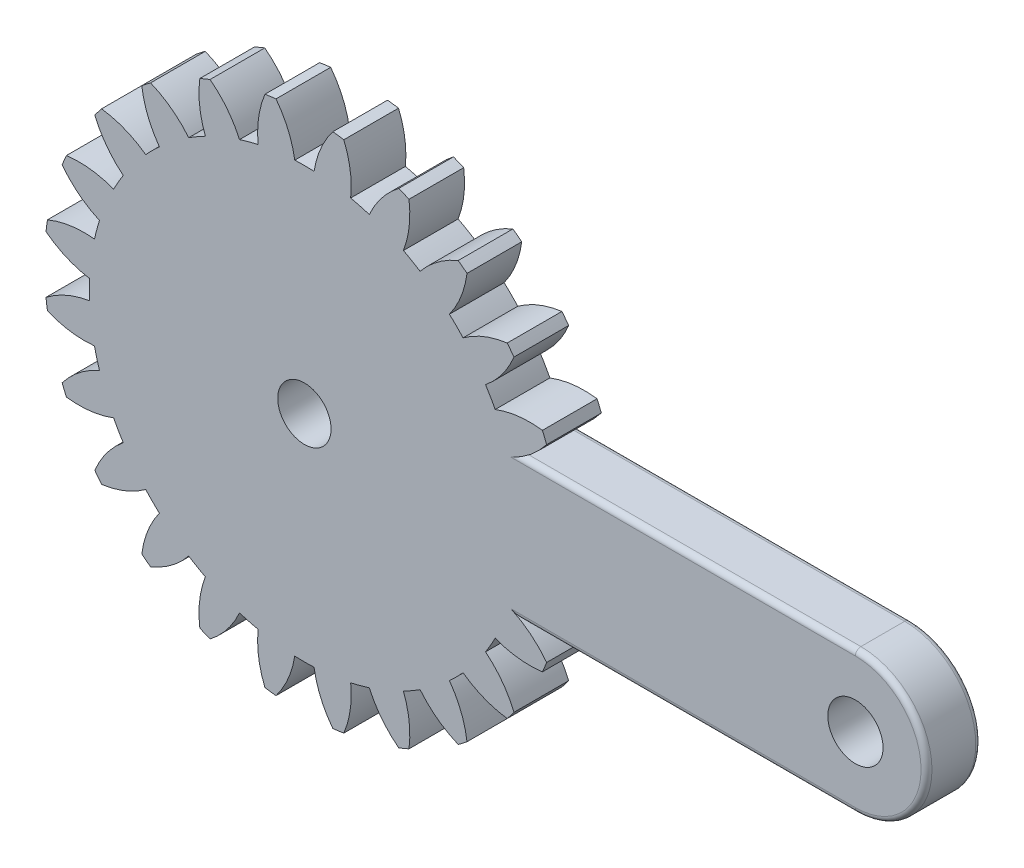
SolidWorks part; units mm, degrees
ref_plane "前视基准面" through (0, 0, 0) normal (0, 0, 1) x (1, 0, 0)
ref_plane "上视基准面" through (0, 0, 0) normal (0, 1, 0) x (1, 0, 0)
ref_plane "右视基准面" through (0, 0, 0) normal (1, 0, 0) x (0, 0, -1)
sketch "草图1" plane through (0, 0, 0) normal (0, 0, 1) x (1, 0, 0)
  line L4 (100.75, 13) -> (39.6109, 13)
  line L5 (39.6109, -13) -> (100.75, -13)
  circle A2 centre (100.75, 0) radius 5.05
  circle A3 centre (0, 0) radius 4.875
  arc A176 (100.75, -13) -> (100.75, 13) centre (100.75, 0) ccw
  arc A177 (39.6109, 13) -> (44.2913, 17.2482) centre (30.3487, 27.9068) ccw
  arc A178 (44.2913, 17.2482) -> (43.515, 19.1224) centre (0, 0) ccw
  arc A179 (43.515, 19.1224) -> (34.8837, 18.1034) centre (41.1928, 1.7267) ccw
  arc A180 (34.8837, 18.1034) -> (33.1198, 21.1585) centre (0, 0) ccw
  arc A181 (33.1198, 21.1585) -> (38.3179, 28.1239) centre (22.0918, 34.8107) ccw
  arc A182 (38.3179, 28.1239) -> (37.083, 29.7333) centre (0, 0) ccw
  arc A183 (37.083, 29.7333) -> (29.0095, 26.5151) centre (39.3423, 12.3293) ccw
  arc A184 (29.0095, 26.5151) -> (26.5151, 29.0095) centre (0, 0) ccw
  arc A185 (26.5151, 29.0095) -> (29.7333, 37.083) centre (12.3293, 39.3423) ccw
  arc A186 (29.7333, 37.083) -> (28.1239, 38.3179) centre (0, 0) ccw
  arc A187 (28.1239, 38.3179) -> (21.1585, 33.1198) centre (34.8107, 22.0918) ccw
  arc A188 (21.1585, 33.1198) -> (18.1034, 34.8837) centre (0, 0) ccw
  arc A189 (18.1034, 34.8837) -> (19.1224, 43.515) centre (1.7267, 41.1928) ccw
  arc A190 (19.1224, 43.515) -> (17.2482, 44.2913) centre (0, 0) ccw
  arc A191 (17.2482, 44.2913) -> (11.8655, 37.4675) centre (27.9068, 30.3487) ccw
  arc A192 (11.8655, 37.4675) -> (8.458, 38.3805) centre (0, 0) ccw
  arc A193 (8.458, 38.3805) -> (7.2083, 46.9815) centre (-8.9937, 40.2361) ccw
  arc A194 (7.2083, 46.9815) -> (5.1971, 47.2463) centre (0, 0) ccw
  arc A195 (5.1971, 47.2463) -> (1.7638, 39.2618) centre (19.1011, 36.5374) ccw
  arc A196 (1.7638, 39.2618) -> (-1.7638, 39.2618) centre (0, 0) ccw
  arc A197 (-1.7638, 39.2618) -> (-5.1971, 47.2463) centre (-19.1011, 36.5374) ccw
  arc A198 (-5.1971, 47.2463) -> (-7.2083, 46.9815) centre (0, 0) ccw
  arc A199 (-7.2083, 46.9815) -> (-8.458, 38.3805) centre (8.9937, 40.2361) ccw
  arc A200 (-8.458, 38.3805) -> (-11.8655, 37.4675) centre (0, 0) ccw
  arc A201 (-11.8655, 37.4675) -> (-17.2482, 44.2913) centre (-27.9068, 30.3487) ccw
  arc A202 (-17.2482, 44.2913) -> (-19.1224, 43.515) centre (0, 0) ccw
  arc A203 (-19.1224, 43.515) -> (-18.1034, 34.8837) centre (-1.7267, 41.1928) ccw
  arc A204 (-18.1034, 34.8837) -> (-21.1585, 33.1198) centre (0, 0) ccw
  arc A205 (-21.1585, 33.1198) -> (-28.1239, 38.3179) centre (-34.8107, 22.0918) ccw
  arc A206 (-28.1239, 38.3179) -> (-29.7333, 37.083) centre (0, 0) ccw
  arc A207 (-29.7333, 37.083) -> (-26.5151, 29.0095) centre (-12.3293, 39.3423) ccw
  arc A208 (-26.5151, 29.0095) -> (-29.0095, 26.5151) centre (0, 0) ccw
  arc A209 (-29.0095, 26.5151) -> (-37.083, 29.7333) centre (-39.3423, 12.3293) ccw
  arc A210 (-37.083, 29.7333) -> (-38.3179, 28.1239) centre (0, 0) ccw
  arc A211 (-38.3179, 28.1239) -> (-33.1198, 21.1585) centre (-22.0918, 34.8107) ccw
  arc A212 (-33.1198, 21.1585) -> (-34.8837, 18.1034) centre (0, 0) ccw
  arc A213 (-34.8837, 18.1034) -> (-43.515, 19.1224) centre (-41.1928, 1.7267) ccw
  arc A214 (-43.515, 19.1224) -> (-44.2913, 17.2482) centre (0, 0) ccw
  arc A215 (-44.2913, 17.2482) -> (-37.4675, 11.8655) centre (-30.3487, 27.9068) ccw
  arc A216 (-37.4675, 11.8655) -> (-38.3805, 8.458) centre (0, 0) ccw
  arc A217 (-38.3805, 8.458) -> (-46.9815, 7.2083) centre (-40.2361, -8.9937) ccw
  arc A218 (-46.9815, 7.2083) -> (-47.2463, 5.1971) centre (0, 0) ccw
  arc A219 (-47.2463, 5.1971) -> (-39.2618, 1.7638) centre (-36.5374, 19.1011) ccw
  arc A220 (-39.2618, 1.7638) -> (-39.2618, -1.7638) centre (0, 0) ccw
  arc A221 (-39.2618, -1.7638) -> (-47.2463, -5.1971) centre (-36.5374, -19.1011) ccw
  arc A222 (-47.2463, -5.1971) -> (-46.9815, -7.2083) centre (0, 0) ccw
  arc A223 (-46.9815, -7.2083) -> (-38.3805, -8.458) centre (-40.2361, 8.9937) ccw
  arc A224 (-38.3805, -8.458) -> (-37.4675, -11.8655) centre (0, 0) ccw
  arc A225 (-37.4675, -11.8655) -> (-44.2913, -17.2482) centre (-30.3487, -27.9068) ccw
  arc A226 (-44.2913, -17.2482) -> (-43.515, -19.1224) centre (0, 0) ccw
  arc A227 (-43.515, -19.1224) -> (-34.8837, -18.1034) centre (-41.1928, -1.7267) ccw
  arc A228 (-34.8837, -18.1034) -> (-33.1198, -21.1585) centre (0, 0) ccw
  arc A229 (-33.1198, -21.1585) -> (-38.3179, -28.1239) centre (-22.0918, -34.8107) ccw
  arc A230 (-38.3179, -28.1239) -> (-37.083, -29.7333) centre (0, 0) ccw
  arc A231 (-37.083, -29.7333) -> (-29.0095, -26.5151) centre (-39.3423, -12.3293) ccw
  arc A232 (-29.0095, -26.5151) -> (-26.5151, -29.0095) centre (0, 0) ccw
  arc A233 (-26.5151, -29.0095) -> (-29.7333, -37.083) centre (-12.3293, -39.3423) ccw
  arc A234 (-29.7333, -37.083) -> (-28.1239, -38.3179) centre (0, 0) ccw
  arc A235 (-28.1239, -38.3179) -> (-21.1585, -33.1198) centre (-34.8107, -22.0918) ccw
  arc A236 (-21.1585, -33.1198) -> (-18.1034, -34.8837) centre (0, 0) ccw
  arc A237 (-18.1034, -34.8837) -> (-19.1224, -43.515) centre (-1.7267, -41.1928) ccw
  arc A238 (-19.1224, -43.515) -> (-17.2482, -44.2913) centre (0, 0) ccw
  arc A239 (-17.2482, -44.2913) -> (-11.8655, -37.4675) centre (-27.9068, -30.3487) ccw
  arc A240 (-11.8655, -37.4675) -> (-8.458, -38.3805) centre (0, 0) ccw
  arc A241 (-8.458, -38.3805) -> (-7.2083, -46.9815) centre (8.9937, -40.2361) ccw
  arc A242 (-7.2083, -46.9815) -> (-5.1971, -47.2463) centre (0, 0) ccw
  arc A243 (-5.1971, -47.2463) -> (-1.7638, -39.2618) centre (-19.1011, -36.5374) ccw
  arc A244 (-1.7638, -39.2618) -> (1.7638, -39.2618) centre (0, 0) ccw
  arc A245 (1.7638, -39.2618) -> (5.1971, -47.2463) centre (19.1011, -36.5374) ccw
  arc A246 (5.1971, -47.2463) -> (7.2083, -46.9815) centre (0, 0) ccw
  arc A247 (7.2083, -46.9815) -> (8.458, -38.3805) centre (-8.9937, -40.2361) ccw
  arc A248 (8.458, -38.3805) -> (11.8655, -37.4675) centre (0, 0) ccw
  arc A249 (11.8655, -37.4675) -> (17.2482, -44.2913) centre (27.9068, -30.3487) ccw
  arc A250 (17.2482, -44.2913) -> (19.1224, -43.515) centre (0, 0) ccw
  arc A251 (19.1224, -43.515) -> (18.1034, -34.8837) centre (1.7267, -41.1928) ccw
  arc A252 (18.1034, -34.8837) -> (21.1585, -33.1198) centre (0, 0) ccw
  arc A253 (21.1585, -33.1198) -> (28.1239, -38.3179) centre (34.8107, -22.0918) ccw
  arc A254 (28.1239, -38.3179) -> (29.7333, -37.083) centre (0, 0) ccw
  arc A255 (29.7333, -37.083) -> (26.5151, -29.0095) centre (12.3293, -39.3423) ccw
  arc A256 (26.5151, -29.0095) -> (29.0095, -26.5151) centre (0, 0) ccw
  arc A257 (29.0095, -26.5151) -> (37.083, -29.7333) centre (39.3423, -12.3293) ccw
  arc A258 (37.083, -29.7333) -> (38.3179, -28.1239) centre (0, 0) ccw
  arc A259 (38.3179, -28.1239) -> (33.1198, -21.1585) centre (22.0918, -34.8107) ccw
  arc A260 (33.1198, -21.1585) -> (34.8837, -18.1034) centre (0, 0) ccw
  arc A261 (34.8837, -18.1034) -> (43.515, -19.1224) centre (41.1928, -1.7267) ccw
  arc A262 (43.515, -19.1224) -> (44.2913, -17.2482) centre (0, 0) ccw
  arc A263 (44.2913, -17.2482) -> (39.6109, -13) centre (30.3487, -27.9068) ccw
  dimension "D1" = 47.5313
  dimension "D2" = 39.3014
  dimension "D3" = 9.75
  dimension "D4" = 100.75
  dimension "D5" = 10.1
  dimension "D6" = 13
extrude "凸台-拉伸1" add sketch "草图1" along normal blind 10
fillet "圆角1" radius 1 6 edges at (70.1805, -13, 0) (113.75, 0, 0) (70.1805, -13, 10) (113.75, 0, 10) (70.1805, 13, 0) (70.1805, 13, 10)
